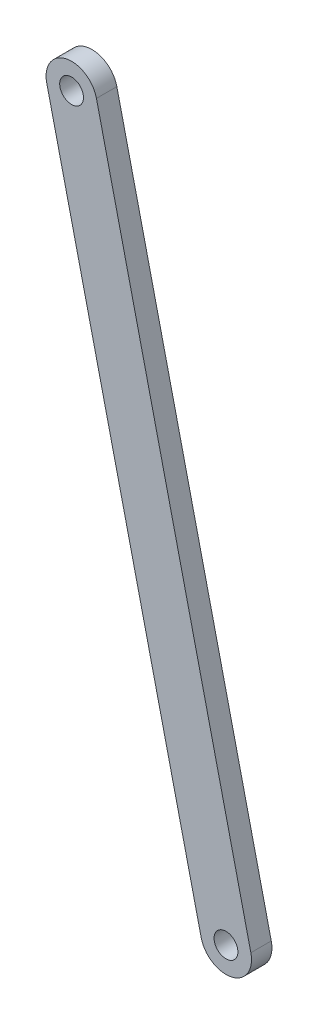
SolidWorks part; units mm, degrees
ref_plane "Front" through (0, 0, 0) normal (0, 0, 1) x (1, 0, 0)
ref_plane "Top" through (0, 0, 0) normal (0, 1, 0) x (1, 0, 0)
ref_plane "Right" through (0, 0, 0) normal (1, 0, 0) x (0, 0, -1)
sketch "Body Driving Dimensions" plane through (0, 0, 0) normal (0, 0, 1) x (1, 0, 0)
  line L0 (0, 0) -> (45.3825, -53.2956)
  line L1 (45.3825, -53.2956) -> (0, -248.0787)
  line L2 (0, -248.0787) -> (-45.3825, -53.2956)
  line L3 (-45.3825, -53.2956) -> (0, 0)
  line L4 (0, 0) -> (0, -36.971) construction
  line L5 (0, 0) -> (149.1516, 57.912)
  line L6 (149.1516, 57.912) -> (45.3825, -53.2956)
  line L7 (0, 0) -> (-199.9092, 53.7151)
  line L8 (-199.9092, 53.7151) -> (-45.3825, -53.2956)
  line L9 (149.1516, 57.912) -> (177.1256, 68.7736) construction
  line L10 (-199.9092, 53.7151) -> (-228.8899, 61.5022) construction
  line L11 (149.1516, 57.912) -> (149.1516, 26.2399) construction
  line L12 (-199.9092, 53.7151) -> (-199.9092, 22.043) construction
  line L13 (0, 0) -> (-98.8336, -98.8336) construction
  line L14 (0, 0) -> (98.8336, -98.8336) construction
  dimension "D1" = 45
  dimension "D2" = 45
sketch "Sketch1" plane through (0, 0, 0) normal (0, 0, 1) x (1, 0, 0)
  line L0 (-45.3825, -53.2956) -> (0, -248.0787) construction
  line L1 (-38.0782, -51.5938) -> (7.3044, -246.3768)
  line L2 (-52.6869, -54.9975) -> (-7.3044, -249.7805)
  circle A0 centre (-45.3825, -53.2956) radius 3.5
  circle A1 centre (0, -248.0787) radius 3.5
  arc A2 (-38.0782, -51.5938) -> (-52.6869, -54.9975) centre (-45.3825, -53.2956) ccw
  arc A3 (-7.3044, -249.7805) -> (7.3044, -246.3768) centre (0, -248.0787) ccw
  point P6 (-22.6913, -150.6871)
  dimension "D1" = 7
  dimension "D2" = 7.5
extrude "Boss-Extrude1" add sketch "Sketch1" along normal blind 6
sketch "Sketch2" [suppressed] plane through (0, 0, 0) normal (0, 0, 1) x (1, 0, 0)
  line L0 (0, 0) -> (70, 0) construction
  line L1 (0, 0) -> (45.3825, -53.2956) construction
  line L2 (68.5536, 7.3592) -> (20.904, -2.0062)
  line L3 (71.4464, -7.3592) -> (4.05, -20.6058)
  circle A0 centre (0, 0) radius 17.5 construction
  circle A1 centre (0, 17.5) radius 1.65
  circle A2 centre (-17.5, 0) radius 1.65
  circle A3 centre (17.5, 0) radius 1.65
  circle A4 centre (0, -17.5) radius 1.65
  circle A5 centre (70, 0) radius 3.5
  circle A6 centre (70, 0) radius 7.5 construction
  circle A7 centre (0, 0) radius 21 construction
  arc A8 (68.5536, 7.3592) -> (71.4464, -7.3592) centre (70, 0) cw
  arc A9 (20.904, -2.0062) -> (4.05, -20.6058) centre (0, 0) ccw
  circle A10 centre (0, 0) radius 5
  dimension "D1" = 3.3
  dimension "D2" = 35
  dimension "D3" = 7
  dimension "D4" = 42
  dimension "D5" = 15
  dimension "D6" = 10
extrude "Boss-Extrude2" [suppressed] add sketch "Sketch2" along normal blind 6
fillet "Fillet1" [suppressed] radius 5
equation "\"l2\"= 200"
equation "\"D3@Body Driving Dimensions\" = \"l2\""
equation "\"l1\"= 70"
equation "\"D4@Body Driving Dimensions\" = \"l1\""
equation "\"s1r\"= 1.94122348320248rad"
equation "\"s2r\"= - 1.833281132rad"
equation "\"offset\"= 10mm"
equation "\"s1_len\"= 0.08m"
equation "\"s2_len\"= 0.127m"
equation "\"s1_anchor_dist\"= \"offset\" + \"l1\" + \"s1_len\""
equation "\"s2_anchor_dist\"= \"offset\" + \"l1\" + \"s2_len\""
equation "\"D5@Body Driving Dimensions\" = \"s1_anchor_dist\""
equation "\"D6@Body Driving Dimensions\" = \"s2_anchor_dist\""
equation "\"D7@Body Driving Dimensions\" = \"s1r\""
equation "\"D8@Body Driving Dimensions\" =  - \"s2r\""
equation "\"carbon_fiber_plate_thickness\"=6"
equation "\"D1@Boss-Extrude1\"=\"carbon_fiber_plate_thickness\""
equation "\"D1@Boss-Extrude2\"=\"carbon_fiber_plate_thickness\""
